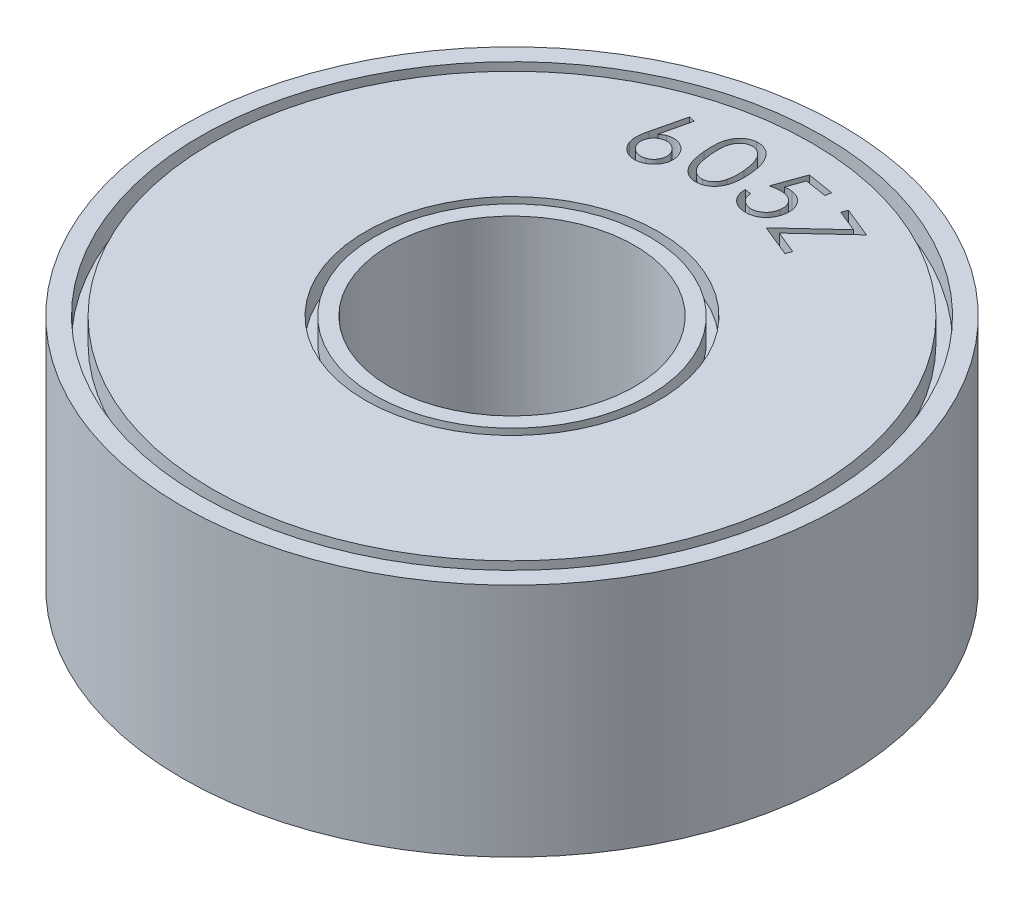
SolidWorks part; units mm, degrees
ref_plane "Front Plane" through (0, 0, 0) normal (0, 0, 1) x (1, 0, 0)
ref_plane "Top Plane" through (0, 0, 0) normal (0, 1, 0) x (1, 0, 0)
ref_plane "Right Plane" through (0, 0, 0) normal (1, 0, 0) x (0, 0, -1)
sketch "Sketch1" plane through (0, 0, 0) normal (0, 1, 0) x (1, 0, 0)
  circle A0 centre (0, 0) radius 7
  circle A1 centre (0, 0) radius 2.6
  dimension "D1" = 5.2
  dimension "D2" = 14
extrude "Boss-Extrude1" add sketch "Sketch1" along normal blind 5
sketch "Sketch2" plane through (0, 5, 0) normal (0, 1, 0) x (1, 0, 0)
  circle A0 centre (0, 0) radius 2.9172
  circle A1 centre (0, 0) radius 3.1074
extrude "Cut-Extrude1" cut sketch "Sketch2" against normal blind 0.5
sketch "Sketch3" plane through (0, 5, 0) normal (0, 1, 0) x (1, 0, 0)
  circle A0 centre (0, 0) radius 6.6143
  circle A1 centre (0, 0) radius 6.365
extrude "Cut-Extrude2" cut sketch "Sketch3" against normal blind 0.5
sketch "Sketch5" plane through (0, 5, 0) normal (0, 1, 0) x (1, 0, 0)
  circle A0 centre (0, 0) radius 3.1074 construction
  spline S0 degree 3 poles (-4.5, 0) (-3.9179, 3.2017) (0.0082, 5.9018) (3.9015, 2.9946) (4.5, 0) knots 0 0 0 0 0.5 1 1 1 1 construction
  text T0 "605Z" font "Century Gothic" height in points 5
  dimension "D1" = 4.5
  dimension "D2" = 4.5
  dimension "D3" = 4.5
extrude "Cut-Extrude3" cut sketch "Sketch5" against normal blind 0.5
sketch "Sketch7" plane through (0, 0, 0) normal (0, -1, 0) x (1, 0, 0)
  circle A0 centre (0, 0) radius 2.825
  circle A1 centre (0, 0) radius 3.0471
  circle A2 centre (0, 0) radius 6.6486
  circle A3 centre (0, 0) radius 6.4696
extrude "Cut-Extrude4" cut sketch "Sketch7" against normal blind 0.5 contours A2 | A3 | A1 | A0
sketch "Sketch8" plane through (0, 0, 0) normal (0, -1, 0) x (-1, 0, 0)
  circle A0 centre (0, 0) radius 3.0471 construction
  circle A1 centre (0, 0) radius 3.0471 construction
  spline S0 degree 3 poles (4.4994, -0.0728) (3.9666, -3.0595) (-0.365, -5.8939) (-3.5179, -3.145) (-4.4995, -0.0689) knots 0 0 0 0 0.506679 1 1 1 1 construction
  text T0 "605Z" font "Century Gothic" height in points 5
  dimension "D1" = 4.5
  dimension "D2" = 4.5
  dimension "D3" = 4.5
extrude "Cut-Extrude5" cut sketch "Sketch8" against normal blind 0.5
